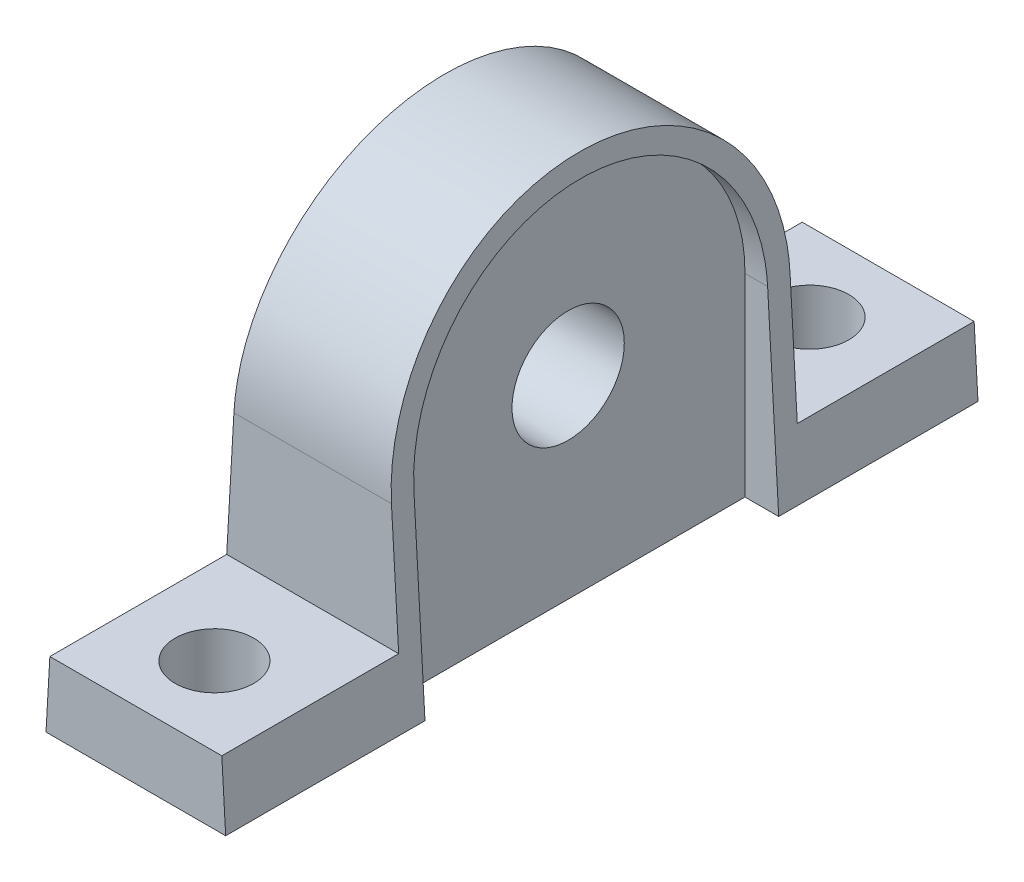
SolidWorks part; units mm, degrees
material "合金钢"
ref_plane "前视基准面" through (0, 0, 0) normal (0, 0, 1) x (1, 0, 0)
ref_plane "上视基准面" through (0, 0, 0) normal (0, 1, 0) x (1, 0, 0)
ref_plane "右视基准面" through (0, 0, 0) normal (1, 0, 0) x (0, 0, -1)
sketch "草图1" plane through (0, 0, 0) normal (0, 0, 1) x (1, 0, 0)
  line L0 (69.2331, 150.4836) -> (329.6081, 150.4836) construction
  line L1 (0, 0) -> (0, 41.7197) construction
  line L2 (8, 0) -> (-8, 0)
  line L3 (-8, 0) -> (-6, 35)
  line L4 (-6, 35) -> (6, 35)
  line L5 (8, 0) -> (6, 35)
  point P9 (0, 35)
  dimension "D1" = 8
  dimension "D2" = 6
  dimension "D3" = 35
extrude "凸台-拉伸1" add sketch "草图1" along normal blind 67
sketch "草图2" plane through (0, 0, 0) normal (1, 0, 0) x (0, 0, -1)
  line L0 (113.5531, 237.8033) -> (549.5531, 237.8033) construction
  line L1 (-33.5, 0) -> (-33.5, 43.4545) construction
  line L2 (-67, 0) -> (0, 0) construction
  line L4 (-67, 6) -> (-51.25, 6)
  line L5 (-67, 0) -> (-67, 35) construction
  line L6 (-51.25, 6) -> (-51.25, 17.25)
  line L7 (-67, 6) -> (-67, 0)
  line L8 (-67, 0) -> (0, 0)
  line L9 (0, 6) -> (0, 0)
  line L10 (0, 6) -> (-15.75, 6)
  line L11 (-15.75, 6) -> (-15.75, 17.25)
  line L12 (-67, 35) -> (0, 35) construction
  line L13 (-67, 6) -> (-67, 35)
  line L14 (-67, 35) -> (0, 35)
  line L15 (0, 35) -> (0, 6)
  arc A0 (-51.25, 17.25) -> (-15.75, 17.25) centre (-33.5, 17.25) cw
  circle A1 centre (-33.5, 17.25) radius 5
  dimension "D3" = 10
  dimension "D1" = 6
  dimension "D2" = 35.5
extrude "切除-拉伸1" cut sketch "草图2" against normal mid plane 30 contours L6 A0 L14 L13 L4 | L14 A0 L11 L10 L15 | A1
ref_plane "基准面1" through (8, 0, 0) normal (1, 0, 0) x (0, 0, -1)
sketch "草图3" plane through (8, 0, 0) normal (1, 0, 0) x (0, 0, -1)
  line L0 (-51.25, 17.25) -> (-51.25, 6) construction
  line L1 (-15.75, 17.25) -> (-15.75, 6) construction
  line L2 (-51.25, 17.25) -> (-51.25, 6)
  line L3 (-15.75, 17.25) -> (-15.75, 6)
  line L4 (-51.25, 6) -> (-51.25, 0)
  line L5 (-67, 0) -> (0, 0) construction
  line L6 (-51.25, 0) -> (-15.75, 0)
  line L7 (-15.75, 0) -> (-15.75, 6)
  line L8 (-49.25, 17.25) -> (-49.25, 6)
  line L9 (-49.25, 6) -> (-49.25, 0)
  line L10 (-17.75, 6) -> (-17.75, 0)
  line L12 (-17.75, 17.25) -> (-17.75, 6)
  line L13 (-49.25, 2) -> (-17.75, 2) construction
  line L14 (-49.25, 6) -> (-49.25, 2) construction
  line L15 (-17.75, 2) -> (-17.75, 6) construction
  arc A0 (-15.75, 17.25) -> (-51.25, 17.25) centre (-33.5, 17.25) ccw construction
  arc A1 (-15.75, 17.25) -> (-51.25, 17.25) centre (-33.5, 17.25) ccw
  arc A2 (-17.75, 17.25) -> (-49.25, 17.25) centre (-33.5, 17.25) ccw
  dimension "D1" = 2
extrude "切除-拉伸2" cut sketch "草图3" against normal blind 3 contours L12 A2 L8 L9 L6 L10
mirror "镜向1" about plane through (0, 0, 0) normal (1, 0, 0) of "切除-拉伸2"
ref_plane "基准面2" through (-10, 0, 0) normal (1, 0, 0) x (0, 0, -1)
sketch "草图4" plane through (-10, 0, 0) normal (1, 0, 0) x (0, 0, -1)
  circle A0 centre (-33.5, 17.25) radius 7
  circle A1 centre (-33.5, 17.25) radius 5 construction
  circle A2 centre (-33.5, 17.25) radius 5
  dimension "D1" = 14
extrude "凸台-拉伸2" add sketch "草图4" along normal up to surface (5 mm away) up to face at (-5, 12.5625, 33.5)
sketch "草图5" plane through (0, 0, 0) normal (0, -1, 0) x (1, 0, 0)
  line L0 (-5, 33.5) -> (5, 33.5) construction
  line L1 (-5, 40.5) -> (-5, 26.5) construction
  line L2 (5, 49.25) -> (5, 17.75) construction
  line L4 (0, 33.5) -> (0, 60) construction
  circle A0 centre (0, 60) radius 3.5
  circle A1 centre (0, 7) radius 3.5
  dimension "D1" = 7
  dimension "D2" = 53
extrude "切除-拉伸4" cut sketch "草图5" against normal blind 10
